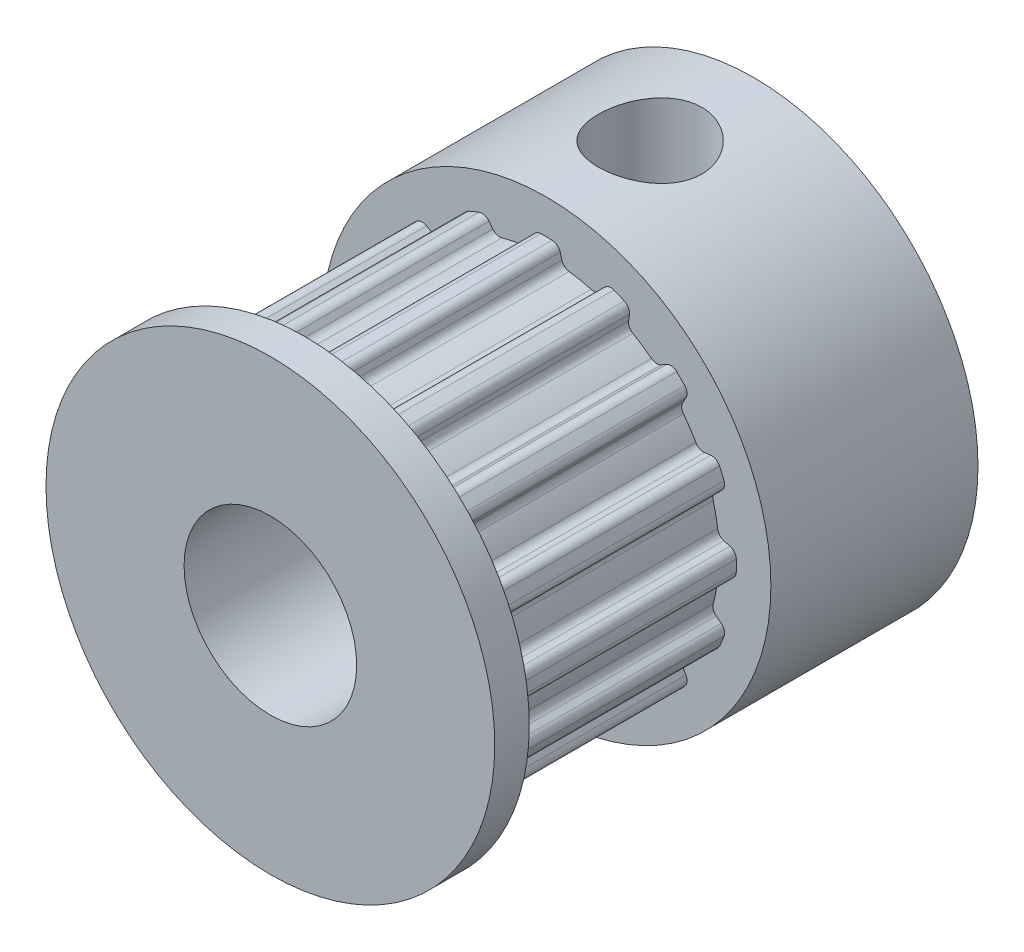
SolidWorks part; units mm, degrees
ref_plane "Front Plane" through (0, 0, 0) normal (0, 0, 1) x (1, 0, 0)
ref_plane "Top Plane" through (0, 0, 0) normal (0, 1, 0) x (1, 0, 0)
ref_plane "Right Plane" through (0, 0, 0) normal (1, 0, 0) x (0, 0, -1)
sketch "Sketch1" plane through (0, 0, 0) normal (0, 0, 1) x (1, 0, 0)
  circle A0 centre (0, 0) radius 2.5
  circle A1 centre (0, 0) radius 6.5
  dimension "D1" = 5
  dimension "D2" = 13
extrude "Boss-Extrude1" add sketch "Sketch1" along normal blind 6
sketch "Sketch2" plane through (0, 0, 6) normal (0, 0, 1) x (1, 0, 0)
  line L0 (0, 5.5) -> (0, 0) construction
  line L1 (0.4455, 5.1389) -> (0.3977, 5.3136)
  line L2 (-0.4455, 5.1389) -> (-0.3977, 5.3136)
  line L3 (2.3782, 4.5773) -> (2.4009, 4.757)
  line L4 (1.555, 4.9182) -> (1.666, 5.0613)
  line L5 (3.9488, 3.3188) -> (4.0385, 3.4761)
  line L6 (3.3188, 3.9488) -> (3.4761, 4.0385)
  line L7 (4.9182, 1.555) -> (5.0613, 1.666)
  line L8 (4.5773, 2.3782) -> (4.757, 2.4009)
  line L9 (5.1389, -0.4455) -> (5.3136, -0.3977)
  line L10 (5.1389, 0.4455) -> (5.3136, 0.3977)
  line L11 (4.5773, -2.3782) -> (4.757, -2.4009)
  line L12 (4.9182, -1.555) -> (5.0613, -1.666)
  line L13 (3.3188, -3.9488) -> (3.4761, -4.0385)
  line L14 (3.9488, -3.3188) -> (4.0385, -3.4761)
  line L15 (1.555, -4.9182) -> (1.666, -5.0613)
  line L16 (2.3782, -4.5773) -> (2.4009, -4.757)
  line L17 (-0.4455, -5.1389) -> (-0.3977, -5.3136)
  line L18 (0.4455, -5.1389) -> (0.3977, -5.3136)
  line L19 (-2.3782, -4.5773) -> (-2.4009, -4.757)
  line L20 (-1.555, -4.9182) -> (-1.666, -5.0613)
  line L21 (-3.9488, -3.3188) -> (-4.0385, -3.4761)
  line L22 (-3.3188, -3.9488) -> (-3.4761, -4.0385)
  line L23 (-4.9182, -1.555) -> (-5.0613, -1.666)
  line L24 (-4.5773, -2.3782) -> (-4.757, -2.4009)
  line L25 (-5.1389, 0.4455) -> (-5.3136, 0.3977)
  line L26 (-5.1389, -0.4455) -> (-5.3136, -0.3977)
  line L27 (-4.5773, 2.3782) -> (-4.757, 2.4009)
  line L28 (-4.9182, 1.555) -> (-5.0613, 1.666)
  line L29 (-3.3188, 3.9488) -> (-3.4761, 4.0385)
  line L30 (-3.9488, 3.3188) -> (-4.0385, 3.4761)
  line L31 (-1.555, 4.9182) -> (-1.666, 5.0613)
  line L32 (-2.3782, 4.5773) -> (-2.4009, 4.757)
  circle A0 centre (0, 0) radius 2.5 construction
  circle A1 centre (0, 0) radius 2.5
  arc A2 (0.164, 5.4976) -> (-0.164, 5.4976) centre (0, 0) ccw
  arc A3 (2.2554, 5.0163) -> (1.9523, 5.1418) centre (0, 0) ccw
  arc A4 (0.4455, 5.1389) -> (0.6539, 4.9571) centre (0.6866, 5.2049) ccw
  arc A5 (0.3977, 5.3136) -> (0.164, 5.4976) centre (0.1566, 5.2477) ccw
  arc A6 (-0.3977, 5.3136) -> (-0.164, 5.4976) centre (-0.1566, 5.2477) cw
  arc A7 (-0.4455, 5.1389) -> (-0.6539, 4.9571) centre (-0.6866, 5.2049) cw
  arc A8 (2.3782, 4.5773) -> (2.5011, 4.3295) centre (2.6262, 4.5459) ccw
  arc A9 (2.4009, 4.757) -> (2.2554, 5.0163) centre (2.1528, 4.7883) ccw
  arc A10 (1.666, 5.0613) -> (1.9523, 5.1418) centre (1.8636, 4.9081) cw
  arc A11 (1.555, 4.9182) -> (1.2928, 4.83) centre (1.3575, 5.0715) cw
  arc A12 (4.0033, 3.7714) -> (3.7714, 4.0033) centre (0, 0) ccw
  arc A13 (3.9488, 3.3188) -> (3.9676, 3.0428) centre (4.1659, 3.1949) ccw
  arc A14 (4.0385, 3.4761) -> (4.0033, 3.7714) centre (3.8214, 3.6) ccw
  arc A15 (3.4761, 4.0385) -> (3.7714, 4.0033) centre (3.6, 3.8214) cw
  arc A16 (3.3188, 3.9488) -> (3.0428, 3.9676) centre (3.1949, 4.1659) cw
  arc A17 (5.1418, 1.9523) -> (5.0163, 2.2554) centre (0, 0) ccw
  arc A18 (4.9182, 1.555) -> (4.83, 1.2928) centre (5.0715, 1.3575) ccw
  arc A19 (5.0613, 1.666) -> (5.1418, 1.9523) centre (4.9081, 1.8636) ccw
  arc A20 (4.757, 2.4009) -> (5.0163, 2.2554) centre (4.7883, 2.1528) cw
  arc A21 (4.5773, 2.3782) -> (4.3295, 2.5011) centre (4.5459, 2.6262) cw
  arc A22 (5.4976, -0.164) -> (5.4976, 0.164) centre (0, 0) ccw
  arc A23 (5.1389, -0.4455) -> (4.9571, -0.6539) centre (5.2049, -0.6866) ccw
  arc A24 (5.3136, -0.3977) -> (5.4976, -0.164) centre (5.2477, -0.1566) ccw
  arc A25 (5.3136, 0.3977) -> (5.4976, 0.164) centre (5.2477, 0.1566) cw
  arc A26 (5.1389, 0.4455) -> (4.9571, 0.6539) centre (5.2049, 0.6866) cw
  arc A27 (5.0163, -2.2554) -> (5.1418, -1.9523) centre (0, 0) ccw
  arc A28 (4.5773, -2.3782) -> (4.3295, -2.5011) centre (4.5459, -2.6262) ccw
  arc A29 (4.757, -2.4009) -> (5.0163, -2.2554) centre (4.7883, -2.1528) ccw
  arc A30 (5.0613, -1.666) -> (5.1418, -1.9523) centre (4.9081, -1.8636) cw
  arc A31 (4.9182, -1.555) -> (4.83, -1.2928) centre (5.0715, -1.3575) cw
  arc A32 (3.7714, -4.0033) -> (4.0033, -3.7714) centre (0, 0) ccw
  arc A33 (3.3188, -3.9488) -> (3.0428, -3.9676) centre (3.1949, -4.1659) ccw
  arc A34 (3.4761, -4.0385) -> (3.7714, -4.0033) centre (3.6, -3.8214) ccw
  arc A35 (4.0385, -3.4761) -> (4.0033, -3.7714) centre (3.8214, -3.6) cw
  arc A36 (3.9488, -3.3188) -> (3.9676, -3.0428) centre (4.1659, -3.1949) cw
  arc A37 (1.9523, -5.1418) -> (2.2554, -5.0163) centre (0, 0) ccw
  arc A38 (1.555, -4.9182) -> (1.2928, -4.83) centre (1.3575, -5.0715) ccw
  arc A39 (1.666, -5.0613) -> (1.9523, -5.1418) centre (1.8636, -4.9081) ccw
  arc A40 (2.4009, -4.757) -> (2.2554, -5.0163) centre (2.1528, -4.7883) cw
  arc A41 (2.3782, -4.5773) -> (2.5011, -4.3295) centre (2.6262, -4.5459) cw
  arc A42 (-0.164, -5.4976) -> (0.164, -5.4976) centre (0, 0) ccw
  arc A43 (-0.4455, -5.1389) -> (-0.6539, -4.9571) centre (-0.6866, -5.2049) ccw
  arc A44 (-0.3977, -5.3136) -> (-0.164, -5.4976) centre (-0.1566, -5.2477) ccw
  arc A45 (0.3977, -5.3136) -> (0.164, -5.4976) centre (0.1566, -5.2477) cw
  arc A46 (0.4455, -5.1389) -> (0.6539, -4.9571) centre (0.6866, -5.2049) cw
  arc A47 (-2.2554, -5.0163) -> (-1.9523, -5.1418) centre (0, 0) ccw
  arc A48 (-2.3782, -4.5773) -> (-2.5011, -4.3295) centre (-2.6262, -4.5459) ccw
  arc A49 (-2.4009, -4.757) -> (-2.2554, -5.0163) centre (-2.1528, -4.7883) ccw
  arc A50 (-1.666, -5.0613) -> (-1.9523, -5.1418) centre (-1.8636, -4.9081) cw
  arc A51 (-1.555, -4.9182) -> (-1.2928, -4.83) centre (-1.3575, -5.0715) cw
  arc A52 (-4.0033, -3.7714) -> (-3.7714, -4.0033) centre (0, 0) ccw
  arc A53 (-3.9488, -3.3188) -> (-3.9676, -3.0428) centre (-4.1659, -3.1949) ccw
  arc A54 (-4.0385, -3.4761) -> (-4.0033, -3.7714) centre (-3.8214, -3.6) ccw
  arc A55 (-3.4761, -4.0385) -> (-3.7714, -4.0033) centre (-3.6, -3.8214) cw
  arc A56 (-3.3188, -3.9488) -> (-3.0428, -3.9676) centre (-3.1949, -4.1659) cw
  arc A57 (-5.1418, -1.9523) -> (-5.0163, -2.2554) centre (0, 0) ccw
  arc A58 (-4.9182, -1.555) -> (-4.83, -1.2928) centre (-5.0715, -1.3575) ccw
  arc A59 (-5.0613, -1.666) -> (-5.1418, -1.9523) centre (-4.9081, -1.8636) ccw
  arc A60 (-4.757, -2.4009) -> (-5.0163, -2.2554) centre (-4.7883, -2.1528) cw
  arc A61 (-4.5773, -2.3782) -> (-4.3295, -2.5011) centre (-4.5459, -2.6262) cw
  arc A62 (-5.4976, 0.164) -> (-5.4976, -0.164) centre (0, 0) ccw
  arc A63 (-5.1389, 0.4455) -> (-4.9571, 0.6539) centre (-5.2049, 0.6866) ccw
  arc A64 (-5.3136, 0.3977) -> (-5.4976, 0.164) centre (-5.2477, 0.1566) ccw
  arc A65 (-5.3136, -0.3977) -> (-5.4976, -0.164) centre (-5.2477, -0.1566) cw
  arc A66 (-5.1389, -0.4455) -> (-4.9571, -0.6539) centre (-5.2049, -0.6866) cw
  arc A67 (-5.0163, 2.2554) -> (-5.1418, 1.9523) centre (0, 0) ccw
  arc A68 (-4.5773, 2.3782) -> (-4.3295, 2.5011) centre (-4.5459, 2.6262) ccw
  arc A69 (-4.757, 2.4009) -> (-5.0163, 2.2554) centre (-4.7883, 2.1528) ccw
  arc A70 (-5.0613, 1.666) -> (-5.1418, 1.9523) centre (-4.9081, 1.8636) cw
  arc A71 (-4.9182, 1.555) -> (-4.83, 1.2928) centre (-5.0715, 1.3575) cw
  arc A72 (-3.7714, 4.0033) -> (-4.0033, 3.7714) centre (0, 0) ccw
  arc A73 (-3.3188, 3.9488) -> (-3.0428, 3.9676) centre (-3.1949, 4.1659) ccw
  arc A74 (-3.4761, 4.0385) -> (-3.7714, 4.0033) centre (-3.6, 3.8214) ccw
  arc A75 (-4.0385, 3.4761) -> (-4.0033, 3.7714) centre (-3.8214, 3.6) cw
  arc A76 (-3.9488, 3.3188) -> (-3.9676, 3.0428) centre (-4.1659, 3.1949) cw
  arc A77 (-1.9523, 5.1418) -> (-2.2554, 5.0163) centre (0, 0) ccw
  arc A78 (-1.555, 4.9182) -> (-1.2928, 4.83) centre (-1.3575, 5.0715) ccw
  arc A79 (-1.666, 5.0613) -> (-1.9523, 5.1418) centre (-1.8636, 4.9081) ccw
  arc A80 (-2.4009, 4.757) -> (-2.2554, 5.0163) centre (-2.1528, 4.7883) cw
  arc A81 (-2.3782, 4.5773) -> (-2.5011, 4.3295) centre (-2.6262, 4.5459) cw
  arc A82 (-0.6539, 4.9571) -> (-1.2928, 4.83) centre (0, 0) ccw
  arc A83 (-2.5011, 4.3295) -> (-3.0428, 3.9676) centre (0, 0) ccw
  arc A84 (-3.9676, 3.0428) -> (-4.3295, 2.5011) centre (0, 0) ccw
  arc A85 (-4.83, 1.2928) -> (-4.9571, 0.6539) centre (0, 0) ccw
  arc A86 (-4.9571, -0.6539) -> (-4.83, -1.2928) centre (0, 0) ccw
  arc A87 (-4.3295, -2.5011) -> (-3.9676, -3.0428) centre (0, 0) ccw
  arc A88 (-3.0428, -3.9676) -> (-2.5011, -4.3295) centre (0, 0) ccw
  arc A89 (-1.2928, -4.83) -> (-0.6539, -4.9571) centre (0, 0) ccw
  arc A90 (0.6539, -4.9571) -> (1.2928, -4.83) centre (0, 0) ccw
  arc A91 (2.5011, -4.3295) -> (3.0428, -3.9676) centre (0, 0) ccw
  arc A92 (3.9676, -3.0428) -> (4.3295, -2.5011) centre (0, 0) ccw
  arc A93 (4.83, -1.2928) -> (4.9571, -0.6539) centre (0, 0) ccw
  arc A94 (4.9571, 0.6539) -> (4.83, 1.2928) centre (0, 0) ccw
  arc A95 (4.3295, 2.5011) -> (3.9676, 3.0428) centre (0, 0) ccw
  arc A96 (1.2928, 4.83) -> (0.6539, 4.9571) centre (0, 0) ccw
  arc A97 (3.0428, 3.9676) -> (2.5011, 4.3295) centre (0, 0) ccw
  point P10 (0.4901, 4.9759)
  point P13 (0.3498, 5.4889)
  point P16 (-0.3498, 5.4889)
  point P19 (-0.4901, 4.9759)
  point P28 (2.357, 4.4096)
  point P35 (1.4514, 4.7847)
  point P42 (3.8651, 3.172)
  point P49 (3.172, 3.8651)
  point P56 (4.7847, 1.4514)
  point P63 (4.4096, 2.357)
  point P70 (4.9759, -0.4901)
  point P77 (4.9759, 0.4901)
  point P84 (4.4096, -2.357)
  point P91 (4.7847, -1.4514)
  point P98 (3.172, -3.8651)
  point P105 (3.8651, -3.172)
  point P112 (1.4514, -4.7847)
  point P119 (2.357, -4.4096)
  point P126 (-0.4901, -4.9759)
  point P133 (0.4901, -4.9759)
  point P140 (-2.357, -4.4096)
  point P147 (-1.4514, -4.7847)
  point P154 (-3.8651, -3.172)
  point P161 (-3.172, -3.8651)
  point P168 (-4.7847, -1.4514)
  point P175 (-4.4096, -2.357)
  point P182 (-4.9759, 0.4901)
  point P189 (-4.9759, -0.4901)
  point P196 (-4.4096, 2.357)
  point P203 (-4.7847, 1.4514)
  point P210 (-3.172, 3.8651)
  point P217 (-3.8651, 3.172)
  point P224 (-1.4514, 4.7847)
  point P231 (-2.357, 4.4096)
  point P232 (0, 0)
  dimension "D1" = 11
  dimension "D2" = 0.25
  dimension "D3" = 16
extrude "Boss-Extrude2" add sketch "Sketch2" along normal blind 7
sketch "Sketch3" plane through (0, 0, 13) normal (0, 0, 1) x (1, 0, 0)
  circle A0 centre (0, 0) radius 2.5 construction
  circle A1 centre (0, 0) radius 2.5
  circle A2 centre (0, 0) radius 6.5
extrude "Boss-Extrude3" add sketch "Sketch3" along normal blind 1
sketch "Sketch4" plane through (0, 0, 0) normal (0, 1, 0) x (1, 0, 0)
  circle A0 centre (0, -3) radius 1.5
  dimension "D1" = 3
  dimension "D2" = 3
extrude "Cut-Extrude1" cut sketch "Sketch4" along normal through all
sketch "Sketch5" plane through (0, 0, 0) normal (1, 0, 0) x (0, 0, -1)
  circle A0 centre (-3, 0) radius 1.5
  dimension "D1" = 3
  dimension "D2" = 3
extrude "Cut-Extrude2" cut sketch "Sketch5" against normal through all
